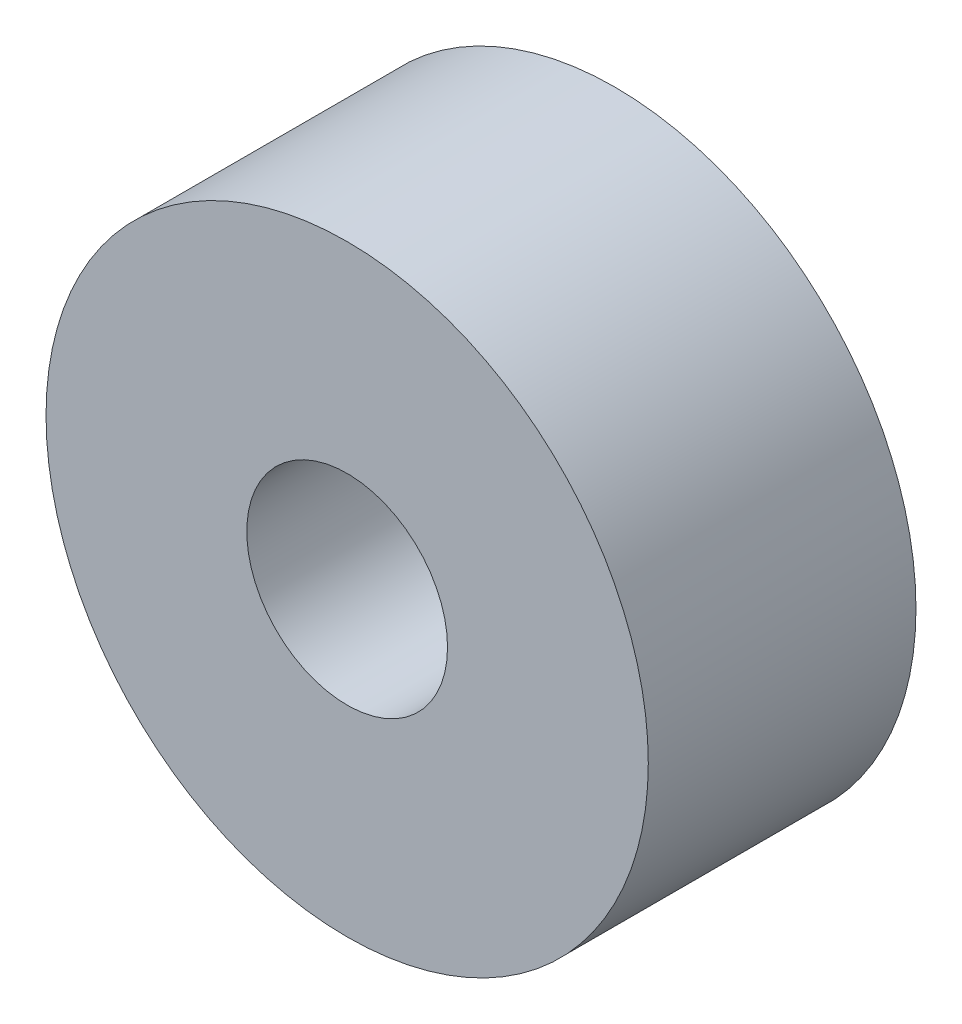
SolidWorks part; units mm, degrees
ref_plane "Ön Düzlem" through (0, 0, 0) normal (0, 0, 1) x (1, 0, 0)
ref_plane "Üst Düzlem" through (0, 0, 0) normal (0, 1, 0) x (1, 0, 0)
ref_plane "Sağ Düzlem" through (0, 0, 0) normal (1, 0, 0) x (0, 0, -1)
sketch "Sketch1" plane through (0, 0, 0) normal (0, 0, 1) x (1, 0, 0)
  circle A0 centre (0, 0) radius 4.5
  circle A1 centre (0, 0) radius 1.5
  dimension "D1" = 9
  dimension "D2" = 3
extrude "Boss-Extrude1" add sketch "Sketch1" along normal blind 4
